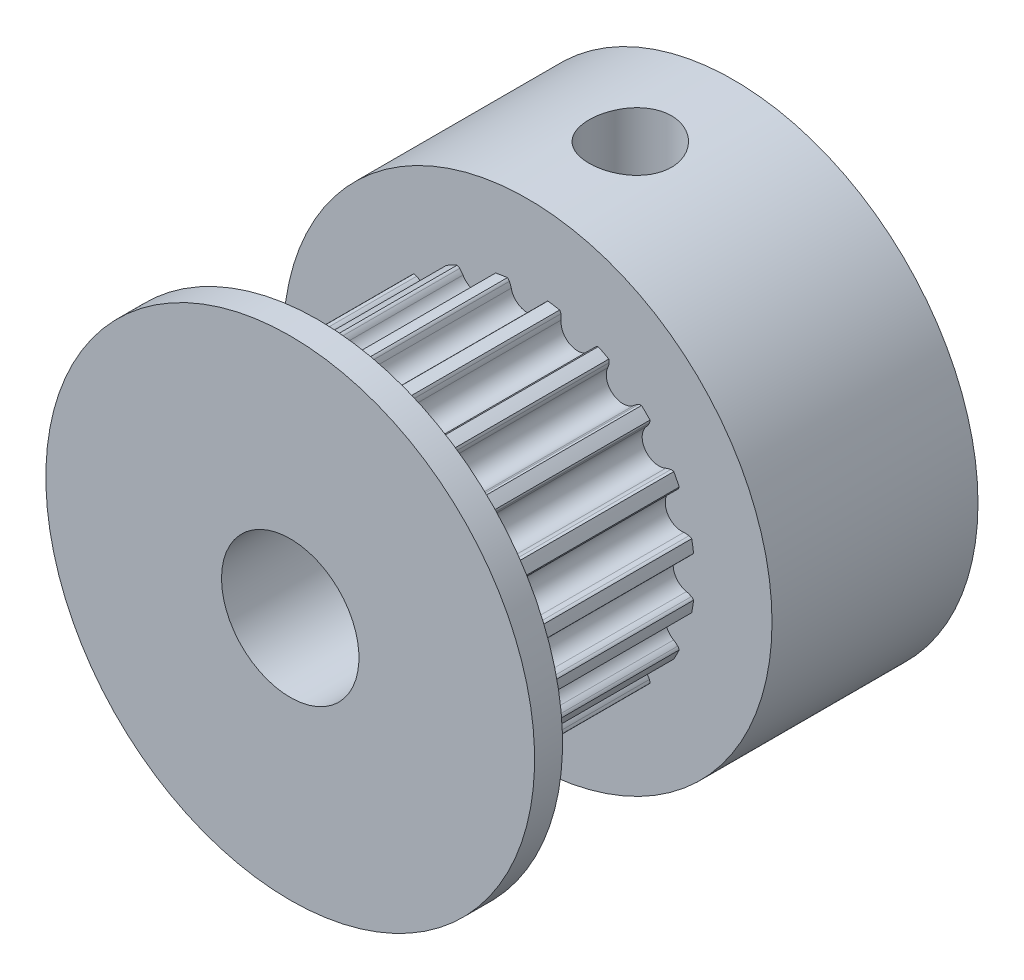
SolidWorks part; units mm, degrees
ref_plane "Alzado" through (0, 0, 0) normal (0, 0, 1) x (1, 0, 0)
ref_plane "Planta" through (0, 0, 0) normal (0, 1, 0) x (1, 0, 0)
ref_plane "Vista lateral" through (0, 0, 0) normal (1, 0, 0) x (0, 0, -1)
ref_plane "Plano1" through (0, 159, 0) normal (0, -1, 0) x (1, 0, 0)
sketch "Croquis1" plane through (0, 159, 0) normal (0, -1, 0) x (1, 0, 0)
  line L0 (124.89, 169.6427) -> (116, 169.6427)
  line L1 (116, 169.6427) -> (116, 162.1497)
  line L2 (116, 162.1497) -> (124.89, 162.1497)
  line L3 (124.89, 162.1497) -> (124.89, 169.6427)
  line L4 (116, 169.6427) -> (116, 162.1497) construction
revolve "Revolución1" add sketch "Croquis1" angle 360 about L4
sketch "Croquis2" plane through (0, 0, 169.6427) normal (0, 0, 1) x (1, 0, 0)
  arc A0 (112.122, 163.3233) -> (113.0867, 164.0242) centre (112.5297, 163.7765) ccw
  arc A1 (113.0867, 164.0242) -> (113.035, 164.2093) centre (113.6901, 164.2926) cw
  arc A2 (113.035, 164.2093) -> (113.0471, 164.317) centre (113.2617, 164.2381) cw
  arc A3 (113.0471, 164.317) -> (113.4341, 164.5141) centre (116, 159) cw
  arc A4 (113.4341, 164.5141) -> (113.5284, 164.4607) centre (113.3718, 164.2942) cw
  arc A5 (113.5284, 164.4607) -> (113.6477, 164.3101) centre (113.076, 163.9796) cw
  arc A6 (113.6477, 164.3101) -> (114.7818, 164.6786) centre (114.1755, 164.6151) ccw
  arc A7 (114.7818, 164.6786) -> (114.7898, 164.8706) centre (115.4386, 164.7473) cw
  arc A8 (114.7898, 164.8706) -> (114.8347, 164.9692) centre (115.0144, 164.8279) cw
  arc A9 (114.8347, 164.9692) -> (115.2637, 165.0372) centre (116, 159) cw
  arc A10 (115.2637, 165.0372) -> (115.3368, 164.9573) centre (115.1364, 164.8473) cw
  arc A11 (115.3368, 164.9573) -> (115.4038, 164.7771) centre (114.7579, 164.6395) cw
  arc A12 (115.4038, 164.7771) -> (116.5962, 164.7771) centre (116, 164.9041) ccw
  arc A13 (116.5962, 164.7771) -> (116.6632, 164.9573) centre (117.2421, 164.6395) cw
  arc A14 (116.6632, 164.9573) -> (116.7363, 165.0372) centre (116.8636, 164.8473) cw
  arc A15 (116.7363, 165.0372) -> (117.1653, 164.9692) centre (116, 159) cw
  arc A16 (117.1653, 164.9692) -> (117.2102, 164.8706) centre (116.9856, 164.8279) cw
  arc A17 (117.2102, 164.8706) -> (117.2182, 164.6786) centre (116.5614, 164.7473) cw
  arc A18 (117.2182, 164.6786) -> (118.3523, 164.3101) centre (117.8245, 164.6151) ccw
  arc A19 (118.3523, 164.3101) -> (118.4716, 164.4607) centre (118.924, 163.9796) cw
  arc A20 (118.4716, 164.4607) -> (118.5659, 164.5141) centre (118.6282, 164.2942) cw
  arc A21 (118.5659, 164.5141) -> (118.9529, 164.317) centre (116, 159) cw
  arc A22 (118.9529, 164.317) -> (118.965, 164.2093) centre (118.7383, 164.2381) cw
  arc A23 (118.965, 164.2093) -> (118.9133, 164.0242) centre (118.3099, 164.2926) cw
  arc A24 (118.9133, 164.0242) -> (119.878, 163.3233) centre (119.4703, 163.7765) ccw
  arc A25 (119.878, 163.3233) -> (120.0381, 163.4297) centre (120.3197, 162.8323) cw
  arc A26 (120.0381, 163.4297) -> (120.1442, 163.4514) centre (120.1356, 163.2229) cw
  arc A27 (120.1442, 163.4514) -> (120.4514, 163.1442) centre (116, 159) cw
  arc A28 (120.4514, 163.1442) -> (120.4297, 163.0381) centre (120.2229, 163.1356) cw
  arc A29 (120.4297, 163.0381) -> (120.3233, 162.878) centre (119.8323, 163.3197) cw
  arc A30 (120.3233, 162.878) -> (121.0242, 161.9133) centre (120.7765, 162.4703) ccw
  arc A31 (121.0242, 161.9133) -> (121.2093, 161.965) centre (121.2926, 161.3099) cw
  arc A32 (121.2093, 161.965) -> (121.317, 161.9529) centre (121.2381, 161.7383) cw
  arc A33 (121.317, 161.9529) -> (121.5141, 161.5659) centre (116, 159) cw
  arc A34 (121.5141, 161.5659) -> (121.4607, 161.4716) centre (121.2942, 161.6282) cw
  arc A35 (121.4607, 161.4716) -> (121.3101, 161.3523) centre (120.9796, 161.924) cw
  arc A36 (121.3101, 161.3523) -> (121.6786, 160.2182) centre (121.6151, 160.8245) ccw
  arc A37 (121.6786, 160.2182) -> (121.8706, 160.2102) centre (121.7473, 159.5614) cw
  arc A38 (121.8706, 160.2102) -> (121.9692, 160.1653) centre (121.8279, 159.9856) cw
  arc A39 (121.9692, 160.1653) -> (122.0372, 159.7363) centre (116, 159) cw
  arc A40 (122.0372, 159.7363) -> (121.9573, 159.6632) centre (121.8473, 159.8636) cw
  arc A41 (121.9573, 159.6632) -> (121.7771, 159.5962) centre (121.6395, 160.2421) cw
  arc A42 (121.7771, 159.5962) -> (121.7771, 158.4038) centre (121.9041, 159) ccw
  arc A43 (121.7771, 158.4038) -> (121.9573, 158.3368) centre (121.6395, 157.7579) cw
  arc A44 (121.9573, 158.3368) -> (122.0372, 158.2637) centre (121.8473, 158.1364) cw
  arc A45 (122.0372, 158.2637) -> (121.9692, 157.8347) centre (116, 159) cw
  arc A46 (121.9692, 157.8347) -> (121.8706, 157.7898) centre (121.8279, 158.0144) cw
  arc A47 (121.8706, 157.7898) -> (121.6786, 157.7818) centre (121.7473, 158.4386) cw
  arc A48 (121.6786, 157.7818) -> (121.3101, 156.6477) centre (121.6151, 157.1755) ccw
  arc A49 (121.3101, 156.6477) -> (121.4607, 156.5284) centre (120.9796, 156.076) cw
  arc A50 (121.4607, 156.5284) -> (121.5141, 156.4341) centre (121.2942, 156.3718) cw
  arc A51 (121.5141, 156.4341) -> (121.317, 156.0471) centre (116, 159) cw
  arc A52 (121.317, 156.0471) -> (121.2093, 156.035) centre (121.2381, 156.2617) cw
  arc A53 (121.2093, 156.035) -> (121.0242, 156.0867) centre (121.2926, 156.6901) cw
  arc A54 (121.0242, 156.0867) -> (120.3233, 155.122) centre (120.7765, 155.5297) ccw
  arc A55 (120.3233, 155.122) -> (120.4297, 154.9619) centre (119.8323, 154.6803) cw
  arc A56 (120.4297, 154.9619) -> (120.4514, 154.8558) centre (120.2229, 154.8644) cw
  arc A57 (120.4514, 154.8558) -> (120.1442, 154.5486) centre (116, 159) cw
  arc A58 (120.1442, 154.5486) -> (120.0381, 154.5703) centre (120.1356, 154.7771) cw
  arc A59 (120.0381, 154.5703) -> (119.878, 154.6767) centre (120.3197, 155.1677) cw
  arc A60 (119.878, 154.6767) -> (118.9133, 153.9758) centre (119.4703, 154.2235) ccw
  arc A61 (118.9133, 153.9758) -> (118.965, 153.7907) centre (118.3099, 153.7074) cw
  arc A62 (118.965, 153.7907) -> (118.9529, 153.683) centre (118.7383, 153.7619) cw
  arc A63 (118.9529, 153.683) -> (118.5659, 153.4859) centre (116, 159) cw
  arc A64 (118.5659, 153.4859) -> (118.4716, 153.5393) centre (118.6282, 153.7058) cw
  arc A65 (118.4716, 153.5393) -> (118.3523, 153.6899) centre (118.924, 154.0204) cw
  arc A66 (118.3523, 153.6899) -> (117.2182, 153.3214) centre (117.8245, 153.3849) ccw
  arc A67 (117.2182, 153.3214) -> (117.2102, 153.1294) centre (116.5614, 153.2527) cw
  arc A68 (117.2102, 153.1294) -> (117.1653, 153.0308) centre (116.9856, 153.1721) cw
  arc A69 (117.1653, 153.0308) -> (116.7363, 152.9628) centre (116, 159) cw
  arc A70 (116.7363, 152.9628) -> (116.6632, 153.0427) centre (116.8636, 153.1527) cw
  arc A71 (116.6632, 153.0427) -> (116.5962, 153.2229) centre (117.2421, 153.3605) cw
  arc A72 (116.5962, 153.2229) -> (115.4038, 153.2229) centre (116, 153.0959) ccw
  arc A73 (115.4038, 153.2229) -> (115.3368, 153.0427) centre (114.7579, 153.3605) cw
  arc A74 (115.3368, 153.0427) -> (115.2637, 152.9628) centre (115.1364, 153.1527) cw
  arc A75 (115.2637, 152.9628) -> (114.8347, 153.0308) centre (116, 159) cw
  arc A76 (114.8347, 153.0308) -> (114.7898, 153.1294) centre (115.0144, 153.1721) cw
  arc A77 (114.7898, 153.1294) -> (114.7818, 153.3214) centre (115.4386, 153.2527) cw
  arc A78 (114.7818, 153.3214) -> (113.6477, 153.6899) centre (114.1755, 153.3849) ccw
  arc A79 (113.6477, 153.6899) -> (113.5284, 153.5393) centre (113.076, 154.0204) cw
  arc A80 (113.5284, 153.5393) -> (113.4341, 153.4859) centre (113.3718, 153.7058) cw
  arc A81 (113.4341, 153.4859) -> (113.0471, 153.683) centre (116, 159) cw
  arc A82 (113.0471, 153.683) -> (113.035, 153.7907) centre (113.2617, 153.7619) cw
  arc A83 (113.035, 153.7907) -> (113.0867, 153.9758) centre (113.6901, 153.7074) cw
  arc A84 (113.0867, 153.9758) -> (112.122, 154.6767) centre (112.5297, 154.2235) ccw
  arc A85 (112.122, 154.6767) -> (111.9619, 154.5703) centre (111.6803, 155.1677) cw
  arc A86 (111.9619, 154.5703) -> (111.8558, 154.5486) centre (111.8644, 154.7771) cw
  arc A87 (111.8558, 154.5486) -> (111.5486, 154.8558) centre (116, 159) cw
  arc A88 (111.5486, 154.8558) -> (111.5703, 154.9619) centre (111.7771, 154.8644) cw
  arc A89 (111.5703, 154.9619) -> (111.6767, 155.122) centre (112.1677, 154.6803) cw
  arc A90 (111.6767, 155.122) -> (110.9758, 156.0867) centre (111.2235, 155.5297) ccw
  arc A91 (110.9758, 156.0867) -> (110.7907, 156.035) centre (110.7074, 156.6901) cw
  arc A92 (110.7907, 156.035) -> (110.683, 156.0471) centre (110.7619, 156.2617) cw
  arc A93 (110.683, 156.0471) -> (110.4859, 156.4341) centre (116, 159) cw
  arc A94 (110.4859, 156.4341) -> (110.5393, 156.5284) centre (110.7058, 156.3718) cw
  arc A95 (110.5393, 156.5284) -> (110.6899, 156.6477) centre (111.0204, 156.076) cw
  arc A96 (110.6899, 156.6477) -> (110.3214, 157.7818) centre (110.3849, 157.1755) ccw
  arc A97 (110.3214, 157.7818) -> (110.1294, 157.7898) centre (110.2527, 158.4386) cw
  arc A98 (110.1294, 157.7898) -> (110.0308, 157.8347) centre (110.1721, 158.0144) cw
  arc A99 (110.0308, 157.8347) -> (109.9628, 158.2637) centre (116, 159) cw
  arc A100 (109.9628, 158.2637) -> (110.0427, 158.3368) centre (110.1527, 158.1364) cw
  arc A101 (110.0427, 158.3368) -> (110.2229, 158.4038) centre (110.3605, 157.7579) cw
  arc A102 (110.2229, 158.4038) -> (110.2229, 159.5962) centre (110.0959, 159) ccw
  arc A103 (110.2229, 159.5962) -> (110.0427, 159.6632) centre (110.3605, 160.2421) cw
  arc A104 (110.0427, 159.6632) -> (109.9628, 159.7363) centre (110.1527, 159.8636) cw
  arc A105 (109.9628, 159.7363) -> (110.0308, 160.1653) centre (116, 159) cw
  arc A106 (110.0308, 160.1653) -> (110.1294, 160.2102) centre (110.1721, 159.9856) cw
  arc A107 (110.1294, 160.2102) -> (110.3214, 160.2182) centre (110.2527, 159.5614) cw
  arc A108 (110.3214, 160.2182) -> (110.6899, 161.3523) centre (110.3849, 160.8245) ccw
  arc A109 (110.6899, 161.3523) -> (110.5393, 161.4716) centre (111.0204, 161.924) cw
  arc A110 (110.5393, 161.4716) -> (110.4859, 161.5659) centre (110.7058, 161.6282) cw
  arc A111 (110.4859, 161.5659) -> (110.683, 161.9529) centre (116, 159) cw
  arc A112 (110.683, 161.9529) -> (110.7907, 161.965) centre (110.7619, 161.7383) cw
  arc A113 (110.7907, 161.965) -> (110.9758, 161.9133) centre (110.7074, 161.3099) cw
  arc A114 (110.9758, 161.9133) -> (111.6767, 162.878) centre (111.2235, 162.4703) ccw
  arc A115 (111.6767, 162.878) -> (111.5703, 163.0381) centre (112.1677, 163.3197) cw
  arc A116 (111.5703, 163.0381) -> (111.5486, 163.1442) centre (111.7771, 163.1356) cw
  arc A117 (111.5486, 163.1442) -> (111.8558, 163.4514) centre (116, 159) cw
  arc A118 (111.8558, 163.4514) -> (111.9619, 163.4297) centre (111.8644, 163.2229) cw
  arc A119 (111.9619, 163.4297) -> (112.122, 163.3233) centre (111.6803, 162.8323) cw
extrude "Saliente-Extruir1" add sketch "Croquis2" along normal blind 7.62
ref_plane "Plano2" through (0, 0, 177.2627) normal (0, 0, -1) x (-1, 0, 0)
sketch "Croquis3" plane through (0, 0, 177.2627) normal (0, 0, -1) x (-1, 0, 0)
  circle A0 centre (-116, 159) radius 8.89
extrude "Saliente-Extruir2" add sketch "Croquis3" against normal blind 1.016
hole_wizard "Taladro1" positions "Croquis5" profile "Croquis4" legacy end condition through all
sketch "Croquis5" plane through (0, 0, 162.1497) normal (0, 0, -1) x (-1, 0, 0)
  point P0 (-116, 159)
sketch "Croquis4" plane through (116, 159, 162.1497) normal (1, 0, 0) x (0, 1, 0)
  line L0 (0, 0) -> (0, 16.129)
  line L1 (0, 16.129) -> (2.5, 16.129)
  line L2 (2.5, 16.129) -> (2.5, 0)
  line L3 (2.5, 0) -> (0, 0)
  line L4 (0, 110) -> (0, -10) construction
  dimension "Diámetro" = 5
  dimension "Profundidad" = 16.129
ref_plane "Plano3" through (0, 161.7991, 0) normal (0, -1, 0) x (-1, 0, 0)
hole_wizard "Taladro2" positions "Croquis7" profile "Croquis6" legacy
sketch "Croquis7" plane through (0, 161.7991, 0) normal (0, -1, 0) x (-1, 0, 0)
  point P0 (-116, -165.9089)
sketch "Croquis6" plane through (116, 161.7991, 165.9089) normal (1, 0, 0) x (0, 0, -1)
  line L0 (0, 0) -> (0, 6.0909)
  line L1 (0, 6.0909) -> (1.4986, 6.0909)
  line L2 (1.4986, 6.0909) -> (1.4986, 0)
  line L3 (1.4986, 0) -> (0, 0)
  line L4 (0, 110) -> (0, -10) construction
  dimension "Diámetro" = 2.9972
  dimension "Profundidad" = 6.0909
ref_plane "Plano4" through (113.2009, 0, 0) normal (1, 0, 0) x (0, 0, -1)
hole_wizard "Taladro3" positions "Croquis9" profile "Croquis8" legacy
sketch "Croquis9" plane through (113.2009, 0, 0) normal (1, 0, 0) x (0, 0, -1)
  point P0 (-165.9089, 159)
sketch "Croquis8" plane through (113.2009, 159, 165.9089) normal (0, 1, 0) x (0, 0, -1)
  line L0 (0, 0) -> (0, 6.0909)
  line L1 (0, 6.0909) -> (1.4986, 6.0909)
  line L2 (1.4986, 6.0909) -> (1.4986, 0)
  line L3 (1.4986, 0) -> (0, 0)
  line L4 (0, 110) -> (0, -10) construction
  dimension "Diámetro" = 2.9972
  dimension "Profundidad" = 6.0909
